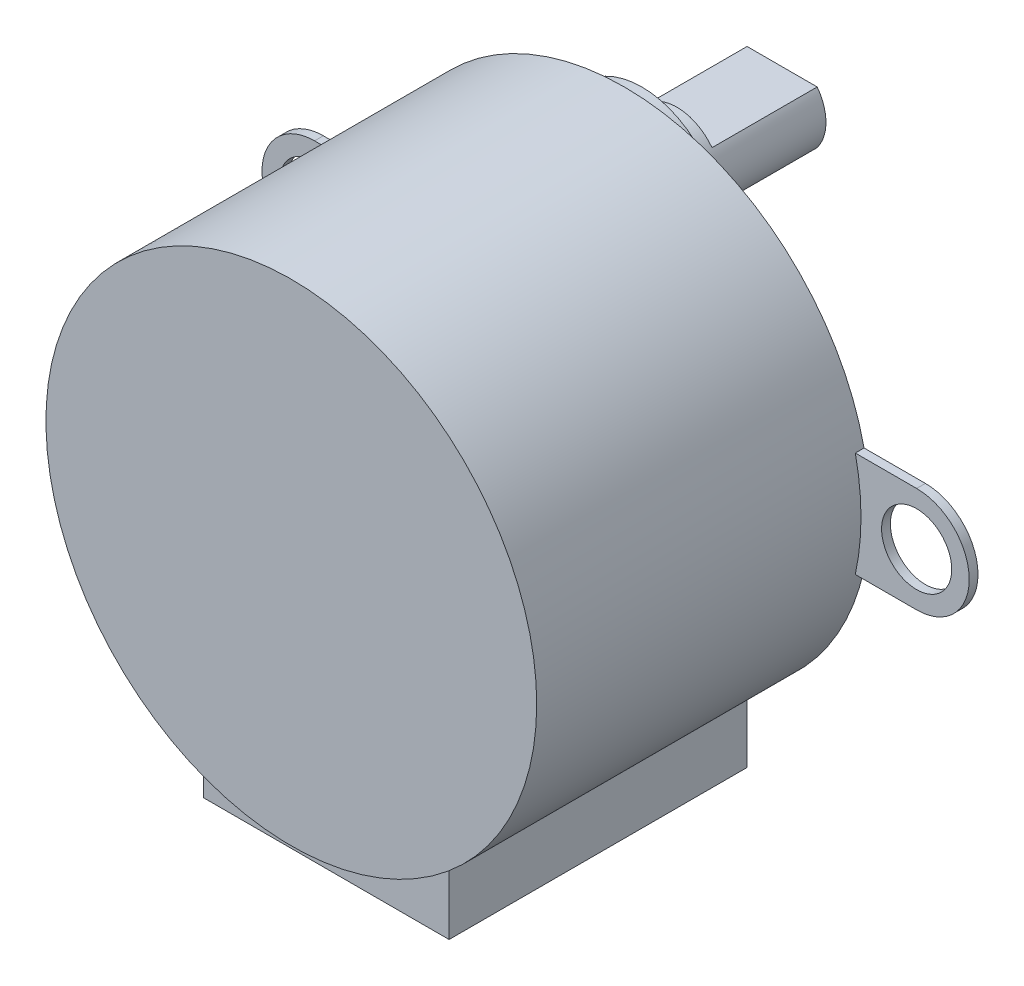
SolidWorks part; units mm, degrees
ref_plane "前视基准面" through (0, 0, 0) normal (0, 0, 1) x (1, 0, 0)
ref_plane "上视基准面" through (0, 0, 0) normal (0, 1, 0) x (1, 0, 0)
ref_plane "右视基准面" through (0, 0, 0) normal (1, 0, 0) x (0, 0, -1)
sketch "Sketch1" plane through (0, 0, 0) normal (0, 0, 1) x (1, 0, 0)
  circle A0 centre (0, 0) radius 14
  dimension "D1" = 28
extrude "Boss-Extrude1" add sketch "Sketch1" along normal blind 19
sketch "Sketch2" plane through (0, 0, 0) normal (0, 0, -1) x (-1, 0, 0)
  line L0 (0, 0) -> (0, 50000) construction
  line L1 (0, 0) -> (-50000, 0) construction
  line L2 (17.1748, 3) -> (13.6748, 3)
  line L3 (17.1748, -3) -> (13.6748, -3)
  line L4 (-17.1748, -3) -> (-13.6748, -3)
  line L5 (-17.1748, 3) -> (-13.6748, 3)
  circle A0 centre (17.1748, 0) radius 2
  arc A1 (17.1748, -3) -> (17.1748, 3) centre (17.1748, 0) ccw
  circle A2 centre (0, 0) radius 14 construction
  circle A3 centre (-17.1748, 0) radius 2
  arc A4 (-17.1748, -3) -> (-17.1748, 3) centre (-17.1748, 0) cw
  arc A5 (-13.6748, 3) -> (-13.6748, -3) centre (0, 0) ccw
  arc A6 (13.6748, -3) -> (13.6748, 3) centre (0, 0) ccw
  dimension "D1" = 4
  dimension "D2" = 6
  dimension "D3" = 3.5
extrude "Boss-Extrude2" add sketch "Sketch2" against normal blind 0.5
sketch "Sketch3" plane through (0, 0, 0) normal (0, 0, -1) x (-1, 0, 0)
  circle A0 centre (0, 9) radius 4.5
  dimension "D1" = 9
  dimension "D2" = 9
extrude "Boss-Extrude3" add sketch "Sketch3" along normal blind 1
sketch "Sketch4" plane through (0, 0, -1) normal (0, 0, -1) x (-1, 0, 0)
  circle A0 centre (0, 9) radius 2.5
  circle A1 centre (0, 9) radius 4.5 construction
  dimension "D1" = 5
extrude "Boss-Extrude4" add sketch "Sketch4" along normal blind 2
sketch "Sketch5" plane through (0, 0, -3) normal (0, 0, -1) x (-1, 0, 0)
  line L0 (-2, 10.5) -> (2, 10.5)
  line L1 (-2, 7.5) -> (2, 7.5)
  circle A0 centre (0, 9) radius 2.5 construction
  circle A1 centre (0, 9) radius 2.5 construction
  arc A2 (-2, 10.5) -> (-2, 7.5) centre (0, 9) ccw
  arc A3 (2, 7.5) -> (2, 10.5) centre (0, 9) ccw
  dimension "D1" = 3
extrude "Boss-Extrude5" add sketch "Sketch5" along normal blind 6
sketch "Sketch6" plane through (0, 0, 0) normal (0, 0, -1) x (-1, 0, 0)
  line L0 (0, 0) -> (0, -16.1244) construction
  line L1 (-7, -16.1244) -> (7, -16.1244)
  line L2 (7, -16.1244) -> (7, -12.1244)
  line L3 (-7, -16.1244) -> (-7, -12.1244)
  line L4 (-7, -12.1244) -> (7, -12.1244)
  arc A0 (-13.6748, -3) -> (13.6748, -3) centre (0, 0) ccw construction
  dimension "D1" = 14
  dimension "D2" = 4
extrude "Boss-Extrude6" add sketch "Sketch6" against normal blind 17
